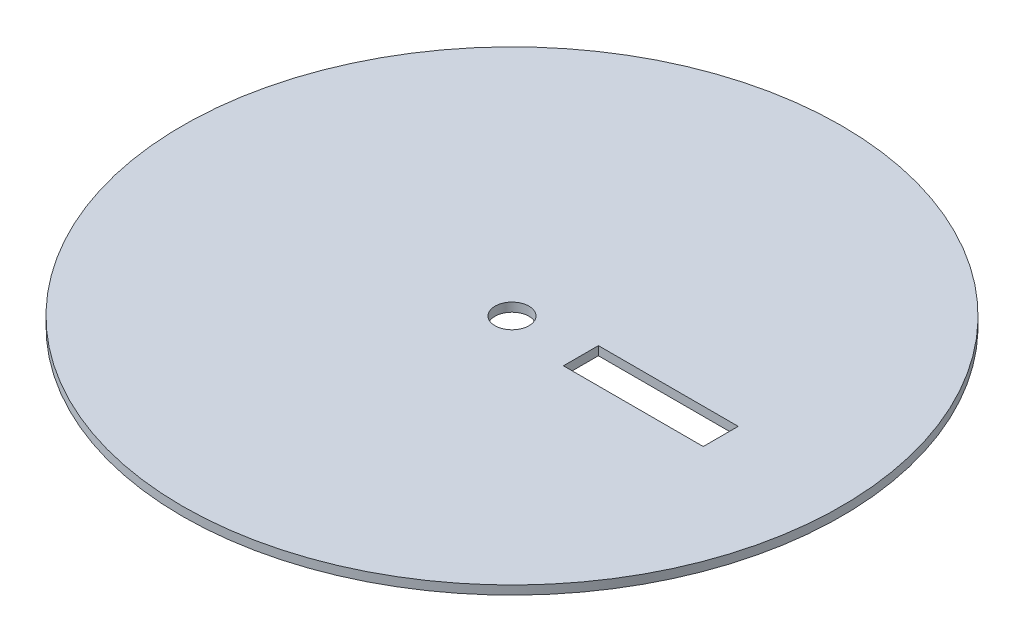
SolidWorks part; units mm, degrees
ref_plane "Front Plane" through (0, 0, 0) normal (0, 0, 1) x (1, 0, 0)
ref_plane "Top Plane" through (0, 0, 0) normal (0, 1, 0) x (1, 0, 0)
ref_plane "Right Plane" through (0, 0, 0) normal (1, 0, 0) x (0, 0, -1)
sketch "Sketch1" plane through (0, 0, 0) normal (0, 1, 0) x (1, 0, 0)
  circle A0 centre (0, 0) radius 16.5
extrude "Boss-Extrude1" add sketch "Sketch1" along normal blind 0.44
sketch "Sketch2" plane through (0, 0.44, 0) normal (0, 1, 0) x (1, 0, 0)
  line L3 (3.45, 0.875) -> (10.45, 0.875)
  line L4 (3.45, 0.875) -> (3.45, -0.875)
  line L5 (3.45, -0.875) -> (10.45, -0.875)
  line L6 (10.45, 0.875) -> (10.45, -0.875)
  circle A0 centre (0, 0) radius 0.85
  point P8 (-4.5509, -0.9755)
  point P9 (0, 0)
extrude "Cut-Extrude1" cut sketch "Sketch2" against normal blind 0.44
